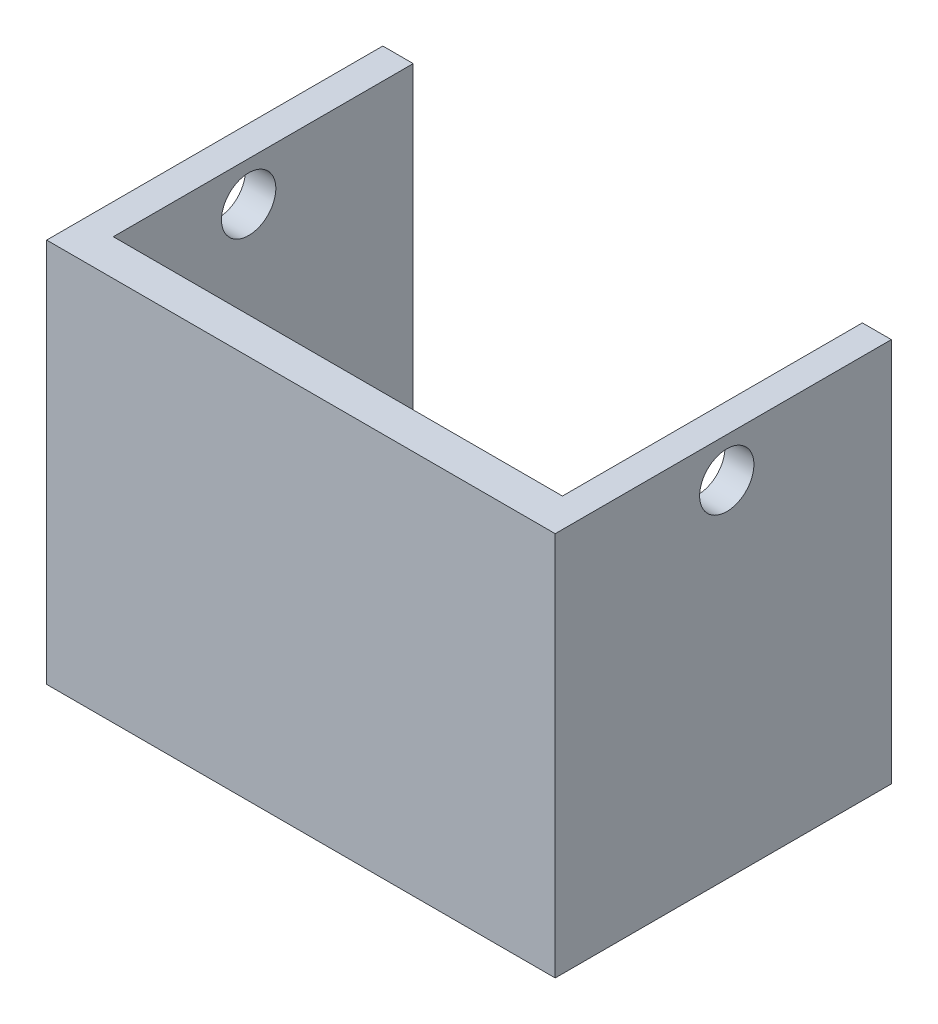
SolidWorks part; units mm, degrees
ref_plane "Alzado" through (0, 0, 0) normal (0, 0, 1) x (1, 0, 0)
ref_plane "Planta" through (0, 0, 0) normal (0, 1, 0) x (1, 0, 0)
ref_plane "Vista lateral" through (0, 0, 0) normal (1, 0, 0) x (0, 0, -1)
sketch "Croquis3" plane through (0, 0, 0) normal (0, 1, 0) x (1, 0, 0)
  line L0 (-33.3884, 0) -> (-33.3884, 39.4244)
  line L1 (-33.3884, 39.4244) -> (-28.6443, 39.4244)
  line L2 (-28.6443, 39.4244) -> (-28.6443, 0)
  line L3 (-28.6443, 0) -> (-28.6443, -7.339)
  line L4 (-28.6443, -7.339) -> (41.3879, -7.339)
  line L5 (41.3879, -7.339) -> (41.3879, 39.4244)
  line L6 (41.3879, 39.4244) -> (45.9061, 39.4244)
  line L7 (45.9061, 39.4244) -> (45.9061, -12.9868)
  line L8 (45.9061, -12.9868) -> (-33.3884, -12.9868)
  line L9 (-33.3884, -12.9868) -> (-33.3884, 0)
extrude "Saliente-Extruir2" add sketch "Croquis3" along normal blind 60
sketch "Croquis4" plane through (-33.3884, 0, 0) normal (-1, 0, 0) x (0, 0, 1)
  circle A0 centre (-13.7639, 53.8444) radius 4.235
extrude "Cortar-Extruir1" cut sketch "Croquis4" against normal blind 110
